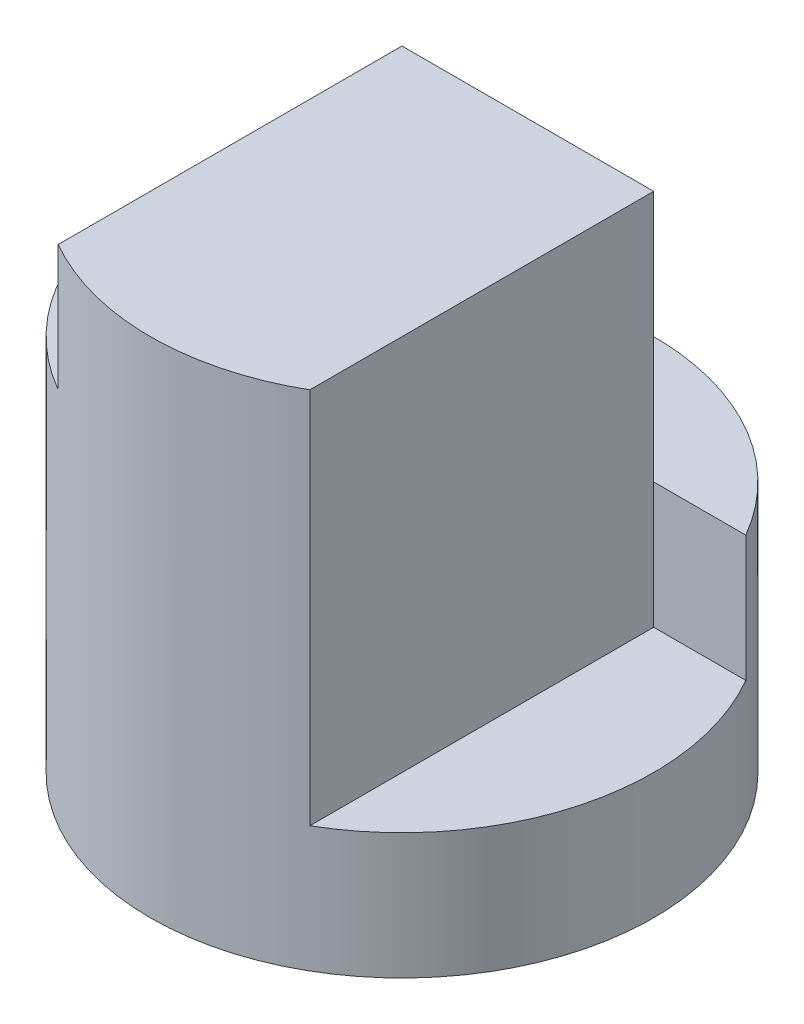
SolidWorks part; units mm, degrees
ref_plane "Front" through (0, 0, 0) normal (0, 0, 1) x (1, 0, 0)
ref_plane "Top" through (0, 0, 0) normal (0, 1, 0) x (1, 0, 0)
ref_plane "Right" through (0, 0, 0) normal (1, 0, 0) x (0, 0, -1)
sketch "Sketch1" plane through (0, 0, 0) normal (0, 1, 0) x (1, 0, 0)
  circle A0 centre (0, 0) radius 2
  dimension "D1" = 4
extrude "Boss-Extrude1" add sketch "Sketch1" along normal blind 4
sketch "Sketch2" plane through (0, 0, 0) normal (0, 0, 1) x (1, 0, 0)
  line L15 (1, 4) -> (1, 1)
  line L16 (2, 4) -> (-2, 4) construction
  line L17 (2, 1) -> (2, 4)
  line L18 (2, 0) -> (2, 4) construction
  line L19 (2, 4) -> (1, 4)
  line L20 (1, 1) -> (2, 1)
  line L22 (-2, 4) -> (-1, 4)
  line L23 (-2, 4) -> (-2, 3)
  line L24 (-2, 3) -> (-1, 3)
  line L25 (-1, 4) -> (-1, 3)
  dimension "D1" = 3
  dimension "D2" = 1
  dimension "D3" = 1
  dimension "D4" = 1
extrude "Cut-Extrude1" cut sketch "Sketch2" against normal blind 1 and the other way blind 3
sketch "Sketch3" plane through (0, 4, 0) normal (0, 1, 0) x (1, 0, 0)
  line L0 (-1.7321, 1) -> (1.7321, 1)
  arc A0 (-1.7321, 1) -> (1.7321, 1) centre (0, 0) cw
  point P5 (0, 0)
  point P6 (0, 0)
extrude "Cut-Extrude2" cut sketch "Sketch3" against normal blind 2
